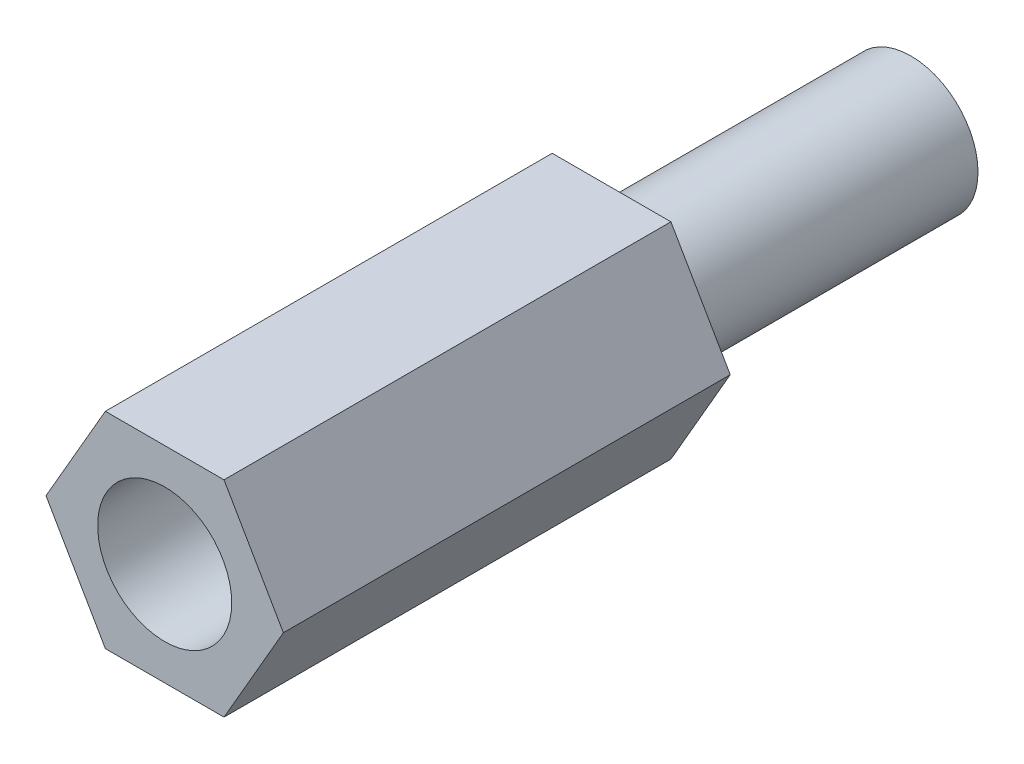
SolidWorks part; units mm, degrees
ref_plane "Alzado" through (0, 0, 0) normal (0, 0, 1) x (1, 0, 0)
ref_plane "Planta" through (0, 0, 0) normal (0, 1, 0) x (1, 0, 0)
ref_plane "Vista lateral" through (0, 0, 0) normal (1, 0, 0) x (0, 0, -1)
sketch "Croquis1" plane through (0, 0, 0) normal (0, 0, 1) x (1, 0, 0)
  line L1 (2.6558, 0) -> (1.3279, 2.3)
  line L2 (1.3279, 2.3) -> (-1.3279, 2.3)
  line L3 (-1.3279, 2.3) -> (-2.6558, 0)
  line L4 (-2.6558, 0) -> (-1.3279, -2.3)
  line L5 (-1.3279, -2.3) -> (1.3279, -2.3)
  line L6 (1.3279, -2.3) -> (2.6558, 0)
  circle A0 centre (0, 0) radius 2.3 construction
  dimension "D1" = 4.6
extrude "Saliente-Extruir1" add sketch "Croquis1" along normal blind 10
sketch "Croquis2" plane through (0, 0, 0) normal (0, 0, -1) x (-1, 0, 0)
  circle A0 centre (0, 0) radius 1.5
  dimension "D1" = 3
extrude "Saliente-Extruir2" add sketch "Croquis2" along normal blind 6.7
sketch "Croquis3" plane through (0, 0, 10) normal (0, 0, 1) x (1, 0, 0)
  circle A0 centre (0, 0) radius 1.5
  dimension "D1" = 3
extrude "Cortar-Extruir1" cut sketch "Croquis3" against normal blind 7
